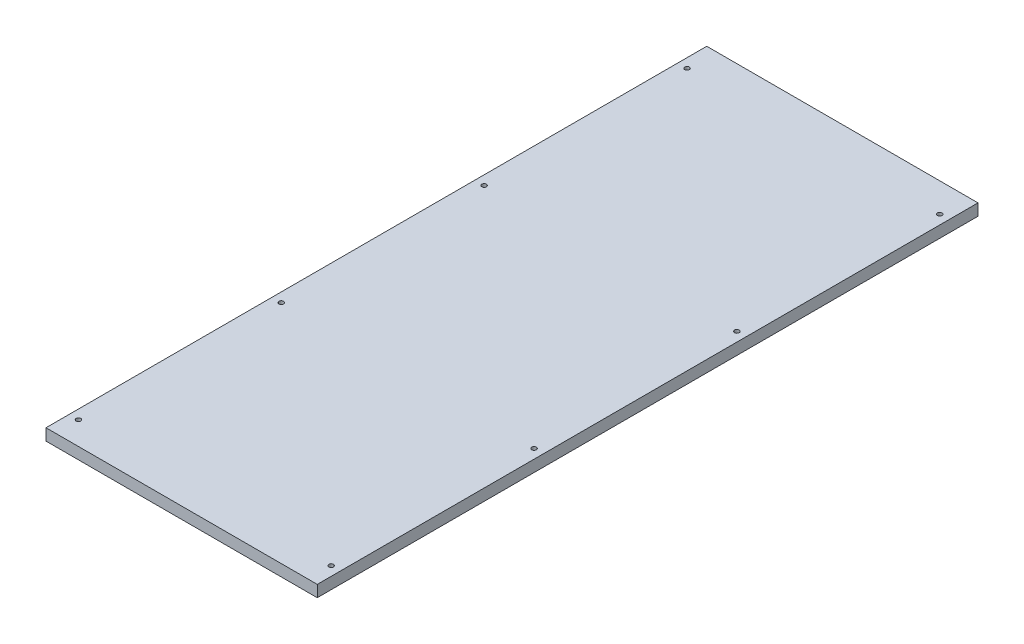
SolidWorks part; units mm, degrees
ref_plane "Front Plane" through (0, 0, 0) normal (0, 0, 1) x (1, 0, 0)
ref_plane "Top Plane" through (0, 0, 0) normal (0, 1, 0) x (1, 0, 0)
ref_plane "Right Plane" through (0, 0, 0) normal (1, 0, 0) x (0, 0, -1)
sketch "Sketch1" plane through (0, 0, 0) normal (0, 1, 0) x (1, 0, 0)
  line L0 (0, 285) -> (0, -285) construction
  line L1 (117, -285) -> (-117, -285)
  line L2 (117, -285) -> (117, 285)
  line L3 (117, 285) -> (-117, 285)
  line L4 (-117, -285) -> (-117, 285)
  circle A0 centre (109, 260) radius 2
  circle A1 centre (109, 85) radius 2
  circle A2 centre (109, -90) radius 2
  circle A3 centre (109, -265) radius 2
  circle A4 centre (-109, -265) radius 2
  circle A5 centre (-109, -90) radius 2
  circle A6 centre (-109, 85) radius 2
  circle A7 centre (-109, 260) radius 2
  point P0 (0, 0)
  point P7 (117, 0)
  point P9 (0, 285)
  dimension "D6" = 4
  dimension "D1" = 234
  dimension "D2" = 570
  dimension "D3" = 8
  dimension "D4" = 25
  dimension "D5" = 4
extrude "Boss-Extrude1" add sketch "Sketch1" along normal blind 10
